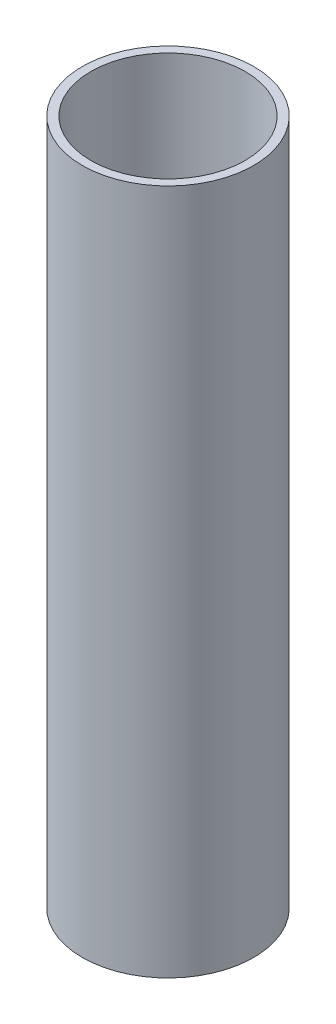
SolidWorks part; units mm, degrees
ref_plane "Front Plane" through (0, 0, 0) normal (0, 0, 1) x (1, 0, 0)
ref_plane "Top Plane" through (0, 0, 0) normal (0, 1, 0) x (1, 0, 0)
ref_plane "Right Plane" through (0, 0, 0) normal (1, 0, 0) x (0, 0, -1)
sketch "Sketch1" plane through (0, 0, 0) normal (0, 1, 0) x (1, 0, 0)
  circle A0 centre (0, 0) radius 45
  circle A1 centre (0, 0) radius 50
  dimension "D1" = 90
  dimension "D2" = 100
extrude "Boss-Extrude1" add sketch "Sketch1" along normal blind 400
